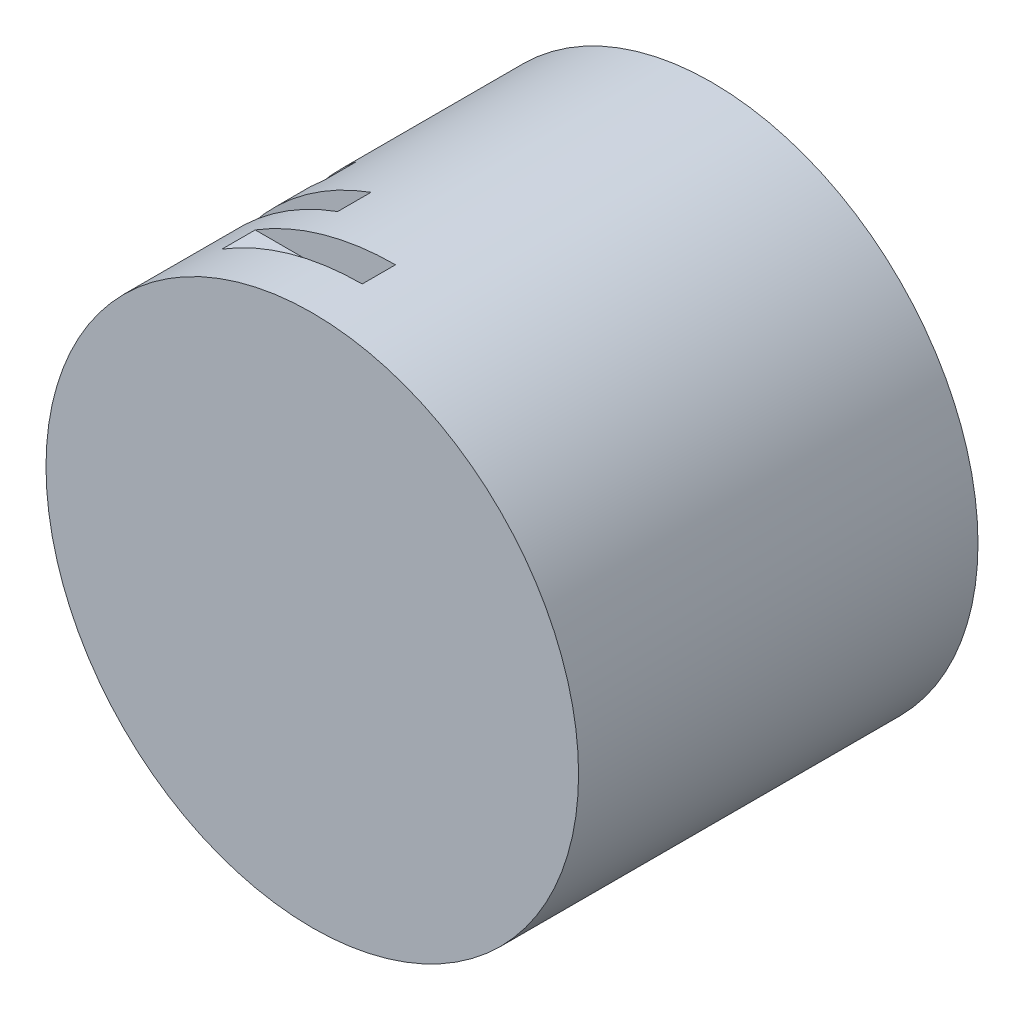
SolidWorks part; units mm, degrees
material "1.0037 (S235JR)"
ref_plane "Vorne" through (0, 0, 0) normal (0, 0, 1) x (1, 0, 0)
ref_plane "Oben" through (0, 0, 0) normal (0, 1, 0) x (1, 0, 0)
ref_plane "Rechts" through (0, 0, 0) normal (1, 0, 0) x (0, 0, -1)
sketch "Skizze1" plane through (0, 0, 0) normal (0, 0, 1) x (1, 0, 0)
  circle A0 centre (0, 0) radius 400
  dimension "D1" = 800
extrude "Aufsatz-Linear austragen1" add sketch "Skizze1" along normal mid plane 600
ref_plane "Ebene1" through (0, 0, 200) normal (0, 0, 1) x (1, 0, 0)
sketch "Skizze2" plane through (0, 0, 200) normal (0, 0, 1) x (1, 0, 0)
  line L0 (0, 400) -> (0, 340)
  line L1 (0, -330) -> (0, 330) construction
  line L2 (0, 340) -> (-210.7131, 340)
  circle A0 centre (0, 0) radius 400 construction
  arc A1 (0, 400) -> (-210.7131, 340) centre (0, 0) ccw
  dimension "D1" = 60
extrude "Schnitt-Linear austragen1" cut sketch "Skizze2" against normal mid plane 50
ref_plane "Ebene2" through (0, 0, 100) normal (0, 0, 1) x (1, 0, 0)
sketch "Skizze3" plane through (0, 0, 100) normal (0, 0, 1) x (1, 0, 0)
  line L0 (0, 0) -> (0, 400) construction
  line L1 (0, 0) -> (-136.8081, 375.877) construction
  line L2 (-136.8081, 375.877) -> (-116.2868, 319.4955)
  line L3 (-116.2868, 319.4955) -> (-314.2924, 247.4274)
  line L4 (0, 340) -> (0, 400) construction
  circle A0 centre (0, 0) radius 400 construction
  arc A1 (-136.8081, 375.877) -> (-314.2924, 247.4274) centre (0, 0) ccw
  dimension "D1" = 20
extrude "Schnitt-Linear austragen2" cut sketch "Skizze3" against normal mid plane 50
sketch "Skizze4" plane through (0, 0, 0) normal (0, 0, 1) x (1, 0, 0)
  line L0 (0, 0) -> (-257.115, 306.4178) construction
  line L1 (0, 0) -> (0, 400) construction
  line L2 (-257.115, 306.4178) -> (-218.5478, 260.4551)
  line L3 (-218.5478, 260.4551) -> (-379.9634, 125.0114)
  line L4 (0, 340) -> (0, 400) construction
  circle A0 centre (0, 0) radius 400 construction
  arc A1 (-257.115, 306.4178) -> (-379.9634, 125.0114) centre (0, 0) ccw
  dimension "D1" = 40
extrude "Schnitt-Linear austragen3" cut sketch "Skizze4" against normal mid plane 50
